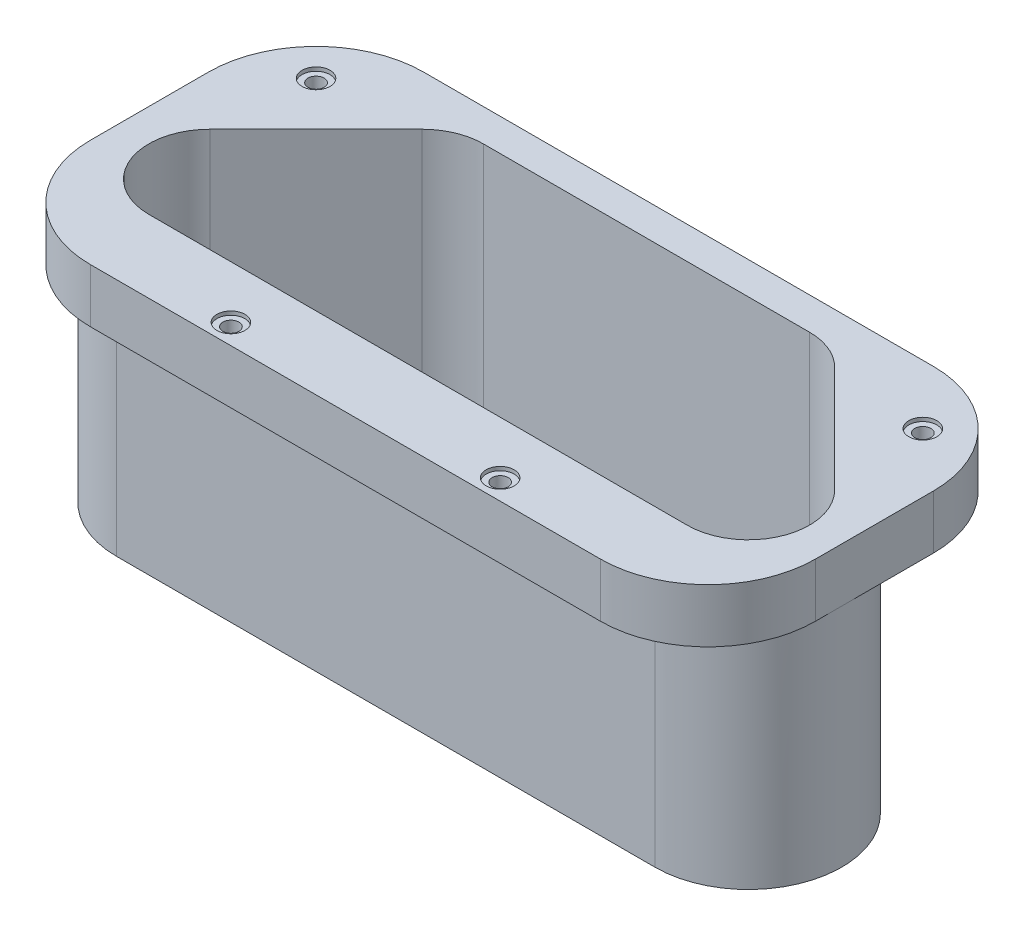
SolidWorks part; units mm, degrees
material "6061-T6 (SS)"
ref_plane "Front Plane" through (0, 0, 0) normal (0, 0, 1) x (1, 0, 0)
ref_plane "Top Plane" through (0, 0, 0) normal (0, 1, 0) x (1, 0, 0)
ref_plane "Right Plane" through (0, 0, 0) normal (1, 0, 0) x (0, 0, -1)
sketch "Sketch1" plane through (0, 0, 0) normal (0, -1, 0) x (1, 0, 0)
  line L1 (-63.5, 21.1234) -> (63.5, 21.1234) construction
  line L2 (72.606, -0.8604) -> (47.5616, -25.9048) construction
  line L3 (-72.606, -0.8604) -> (-47.5616, -25.9048) construction
  line L4 (-38.4556, -29.6766) -> (38.4556, -29.6766) construction
  line L9 (-73.6836, -1.938) -> (-48.6392, -26.9824)
  line L10 (-38.4556, -31.2006) -> (38.4556, -31.2006)
  line L11 (73.6836, -1.938) -> (48.6392, -26.9824)
  line L12 (-63.5, 22.6474) -> (63.5, 22.6474)
  line L14 (-47.5616, -25.9048) -> (-48.6392, -26.9824) construction
  line L15 (-61.1614, -14.4602) -> (-73.2848, -26.5836) construction
  line L16 (-72.606, -0.8604) -> (-73.6836, -1.938) construction
  line L17 (61.1614, -14.4602) -> (73.2848, -26.5836) construction
  line L19 (72.606, -0.8604) -> (73.6836, -1.938) construction
  line L20 (47.5616, -25.9048) -> (48.6392, -26.9824) construction
  line L21 (0, 22.6474) -> (0, 39.7924) construction
  line L22 (48.6392, -26.9824) -> (60.2462, -38.5894) construction
  line L24 (-77.9018, 8.2456) -> (-77.9018, -31.2006) construction
  line L25 (77.9018, 8.2456) -> (77.9018, -38.8206) construction
  line L26 (-85.5218, -38.8206) -> (85.5218, -38.8206)
  line L27 (85.5218, -38.8206) -> (85.5218, 39.7924)
  line L28 (85.5218, 39.7924) -> (-85.5218, 39.7924)
  line L29 (-85.5218, 39.7924) -> (-85.5218, -38.8206)
  arc A0 (-63.5, 21.1234) -> (-72.606, -0.8604) centre (-63.5, 8.2456) ccw construction
  arc A1 (72.606, -0.8604) -> (63.5, 21.1234) centre (63.5, 8.2456) ccw construction
  arc A2 (-47.5616, -25.9048) -> (-38.4556, -29.6766) centre (-38.4556, -16.7988) ccw construction
  arc A3 (38.4556, -29.6766) -> (47.5616, -25.9048) centre (38.4556, -16.7988) ccw construction
  arc A8 (-63.5, 22.6474) -> (-73.6836, -1.938) centre (-63.5, 8.2456) ccw
  arc A9 (-48.6392, -26.9824) -> (-38.4556, -31.2006) centre (-38.4556, -16.7988) ccw
  arc A10 (38.4556, -31.2006) -> (48.6392, -26.9824) centre (38.4556, -16.7988) ccw
  arc A11 (73.6836, -1.938) -> (63.5, 22.6474) centre (63.5, 8.2456) ccw
  dimension "D2" = 25.7556
  dimension "D11" = 7.62
  dimension "D1" = 127
  dimension "D3" = 50.8
  dimension "D4" = 90
  dimension "D7" = 22.6474
  dimension "D8" = 72.606
  dimension "D5" = 17.145
  dimension "D6" = 17.145
  dimension "D9" = 17.145
  dimension "D10" = 7.62
extrude "Boss-Extrude1" add sketch "Sketch1" along normal blind 58.42
sketch "Sketch2" plane through (0, -58.42, 0) normal (0, -1, 0) x (1, 0, 0)
  line L2 (-85.5218, -38.8206) -> (85.5218, -38.8206)
  line L3 (-85.5218, -38.8206) -> (-85.5218, 39.7924)
  line L4 (-85.5218, 39.7924) -> (-85.5218, -38.8206)
  line L5 (-85.5218, 39.7924) -> (-85.5218, -38.8206)
  line L6 (85.5218, -38.8206) -> (85.5218, 39.7924)
  line L7 (-85.5218, -38.8206) -> (85.5218, -38.8206)
  line L11 (-85.5218, -38.8206) -> (85.5218, -38.8206)
  line L12 (-85.5218, 39.7924) -> (85.5218, 39.7924)
  line L13 (85.5218, -38.8206) -> (85.5218, 39.7924)
  line L30 (-79.0718, -7.3262) -> (-54.0274, -32.3706)
  line L31 (-38.4556, -38.8206) -> (38.4556, -38.8206)
  line L32 (54.0274, -32.3706) -> (79.0718, -7.3262)
  line L33 (63.5, 30.2674) -> (-63.5, 30.2674)
  line L34 (-79.0718, -7.3262) -> (-54.0274, -32.3706)
  line L35 (-38.4556, -38.8206) -> (38.4556, -38.8206)
  line L36 (54.0274, -32.3706) -> (79.0718, -7.3262)
  line L37 (63.5, 30.2674) -> (-63.5, 30.2674)
  line L38 (85.5218, -38.8206) -> (85.5218, 39.7924)
  line L39 (85.5218, 39.7924) -> (-85.5218, 39.7924)
  line L40 (85.5218, 39.7924) -> (-85.5218, 39.7924)
  arc A0 (-85.5218, 8.2456) -> (-79.0718, -7.3262) centre (-63.5, 8.2456) ccw
  arc A1 (85.5218, 8.2456) -> (63.5, 30.2674) centre (63.5, 8.2456) ccw
  arc A31 (-54.0274, -32.3706) -> (-38.4556, -38.8206) centre (-38.4556, -16.7988) ccw
  arc A32 (38.4556, -38.8206) -> (54.0274, -32.3706) centre (38.4556, -16.7988) ccw
  arc A33 (79.0718, -7.3262) -> (63.5, 30.2674) centre (63.5, 8.2456) ccw
  arc A34 (-63.5, 30.2674) -> (-79.0718, -7.3262) centre (-63.5, 8.2456) ccw
  arc A35 (-54.0274, -32.3706) -> (-38.4556, -38.8206) centre (-38.4556, -16.7988) ccw
  arc A36 (38.4556, -38.8206) -> (54.0274, -32.3706) centre (38.4556, -16.7988) ccw
  arc A37 (79.0718, -7.3262) -> (85.5218, 8.2456) centre (63.5, 8.2456) ccw
  arc A38 (-63.5, 30.2674) -> (-85.5218, 8.2456) centre (-63.5, 8.2456) ccw
  line M24 (-85.5218, -38.8206) -> (85.5218, -38.8206)
  line M33 (-85.5218, 39.7924) -> (-85.5218, -38.8206)
  line M34 (85.5218, -38.8206) -> (85.5218, 39.7924)
  line M35 (85.5218, 39.7924) -> (-85.5218, 39.7924)
  dimension "D1" = 0
  dimension "D2" = 7.62
extrude "Cut-Extrude1" cut sketch "Sketch2" against normal offset from surface (45.72 mm away) 12.7 contours A37 L36 A36 M24 M34 | A35 L34 A0 L5 M24 | A38 L37 A1 L38 M35 M33 up to face at (0, 0, 0.4859)
sketch "Sketch3" plane through (0, -58.42, 0) normal (0, -1, 0) x (1, 0, 0)
  line L8 (-79.0718, -7.3262) -> (-54.0274, -32.3706) construction
  line L9 (63.5, 30.2674) -> (-63.5, 30.2674) construction
  line L10 (54.0274, -32.3706) -> (79.0718, -7.3262) construction
  line L11 (-38.4556, -38.8206) -> (38.4556, -38.8206) construction
  line L12 (-79.0718, -7.3262) -> (-54.0274, -32.3706)
  line L13 (63.5, 30.2674) -> (-63.5, 30.2674)
  line L14 (54.0274, -32.3706) -> (79.0718, -7.3262)
  line L15 (-38.4556, -38.8206) -> (38.4556, -38.8206)
  arc A8 (-54.0274, -32.3706) -> (-38.4556, -38.8206) centre (-38.4556, -16.7988) ccw construction
  arc A9 (-63.5, 30.2674) -> (-79.0718, -7.3262) centre (-63.5, 8.2456) ccw construction
  arc A10 (79.0718, -7.3262) -> (63.5, 30.2674) centre (63.5, 8.2456) ccw construction
  arc A11 (38.4556, -38.8206) -> (54.0274, -32.3706) centre (38.4556, -16.7988) ccw construction
  arc A12 (-54.0274, -32.3706) -> (-38.4556, -38.8206) centre (-38.4556, -16.7988) ccw
  arc A13 (-63.5, 30.2674) -> (-79.0718, -7.3262) centre (-63.5, 8.2456) ccw
  arc A14 (79.0718, -7.3262) -> (63.5, 30.2674) centre (63.5, 8.2456) ccw
  arc A15 (38.4556, -38.8206) -> (54.0274, -32.3706) centre (38.4556, -16.7988) ccw
extrude "Boss-Extrude2" add sketch "Sketch3" along normal blind 7.62
fillet "Fillet1" radius 25.4 4 edges at (85.5218, -6.35, -38.8206) (85.5218, -6.35, 39.7924) (-85.5218, -6.35, 39.7924) (-85.5218, -6.35, -38.8206)
hole_wizard "#6 Clearance Hole2" positions "Sketch9" profile "Sketch10" hole size "#6" standard "ANSI Inch" end condition through all
sketch "Sketch9" plane through (0, -12.7, 0) normal (0, -1, 0) x (-1, 0, 0)
  line L0 (-85.5218, -8.2456) -> (-85.5218, 13.4206) construction
  line L5 (60.1218, -39.7924) -> (-60.1218, -39.7924) construction
  line L6 (-60.1218, 38.8206) -> (-38.4556, 38.8206) construction
  point P0 (-31.75, -35.0299)
  point P18 (-71.5518, 24.8506)
  dimension "D1" = 53.7718
  dimension "D3" = 4.7625
  dimension "D4" = 13.97
  dimension "D5" = 13.97
sketch "Sketch10" plane through (31.75, -12.7, 35.0299) normal (1, 0, 0) x (0, 0, -1)
  line L0 (0, 0) -> (0, 12.7)
  line L1 (0, 12.7) -> (1.8986, 12.7)
  line L2 (1.8986, 12.7) -> (1.8986, 0)
  line L5 (1.8986, 0) -> (0, 0)
  line L11 (0, -6.35) -> (0, 107.95) construction
  dimension "Thru Hole Dia." = 3.7973
  dimension "Thru Hole Depth" = 12.7
mirror "Mirror1" about plane through (0, 0, 0) normal (1, 0, 0) of "#6 Clearance Hole2"
sketch "Sketch12" plane through (0, 0, 0) normal (0, 1, 0) x (1, 0, 0)
  circle A0 centre (-71.5518, 24.8506) radius 3.302
  circle A1 centre (-31.75, -35.0299) radius 3.302
  circle A2 centre (31.75, -35.0299) radius 3.302
  circle A3 centre (71.5518, 24.8506) radius 3.302
  dimension "D2" = 6.604
extrude "Cut-Extrude2" cut sketch "Sketch12" against normal blind 0.889
